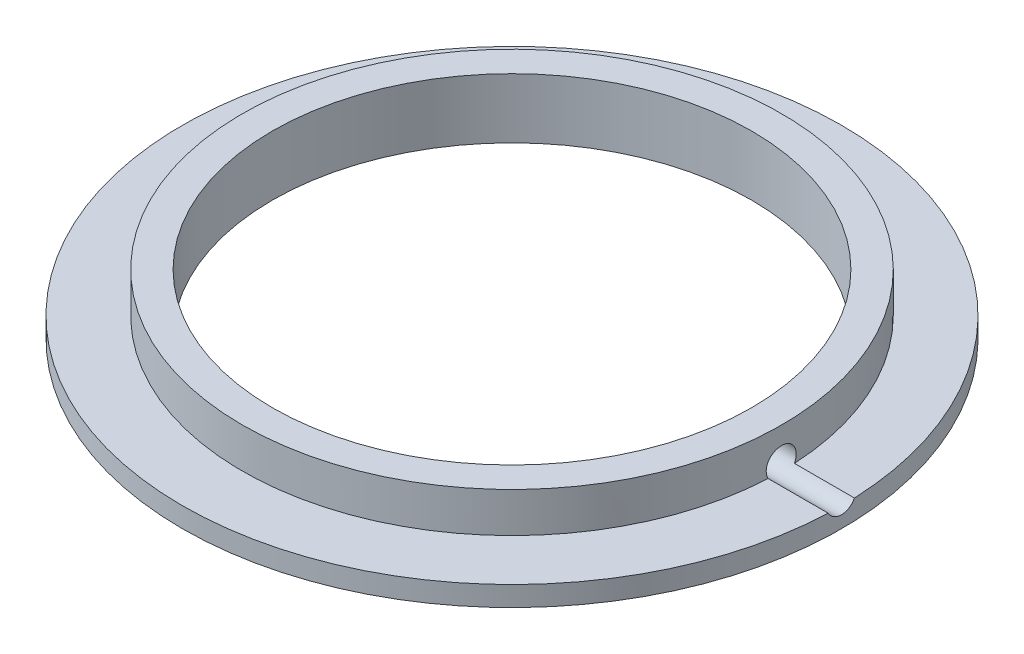
SolidWorks part; units mm, degrees
material "BUTYL"
ref_plane "Front Plane" through (0, 0, 0) normal (0, 0, 1) x (1, 0, 0)
ref_plane "Top Plane" through (0, 0, 0) normal (0, 1, 0) x (1, 0, 0)
ref_plane "Right Plane" through (0, 0, 0) normal (1, 0, 0) x (0, 0, -1)
sketch "Sketch1" plane through (0, 0, 0) normal (0, 1, 0) x (1, 0, 0)
  circle A0 centre (0, 0) radius 16.5
extrude "Boss-Extrude1" add sketch "Sketch1" along normal blind 1
sketch "Sketch2" plane through (0, 0, 0) normal (0, 1, 0) x (1, 0, 0)
  circle A0 centre (0, 0) radius 13.5
extrude "Boss-Extrude2" add sketch "Sketch2" along normal blind 3
sketch "Sketch3" plane through (0, 0, 0) normal (0, 1, 0) x (1, 0, 0)
  circle A0 centre (0, 0) radius 12
extrude "Cut-Extrude1" cut sketch "Sketch3" along normal blind 3
sketch "Sketch5" plane through (0, 0, 0) normal (1, 0, 0) x (0, 0, -1)
  circle A0 centre (0, 1.36) radius 0.75
extrude "Cut-Extrude3" cut sketch "Sketch5" along normal blind 17
